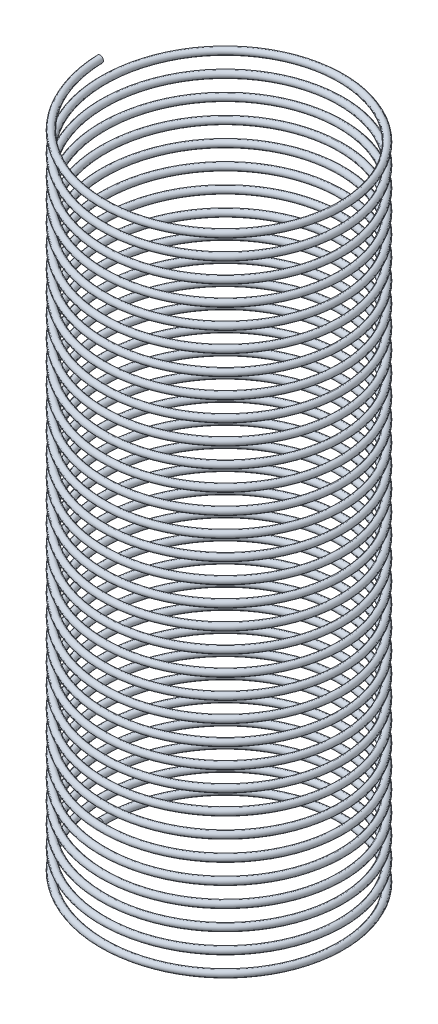
SolidWorks part; units mm, degrees
ref_plane "Front Plane" through (0, 0, 0) normal (0, 0, 1) x (1, 0, 0)
ref_plane "Top Plane" through (0, 0, 0) normal (0, 1, 0) x (1, 0, 0)
ref_plane "Right Plane" through (0, 0, 0) normal (1, 0, 0) x (0, 0, -1)
sketch "Sketch3" plane through (0, 0, 0) normal (0, 1, 0) x (1, 0, 0)
  circle A0 centre (0, 0) radius 17.8101
  dimension "D1" = 35.6203
curve "Helix/Spiral2" pitch 3 height 99 turns 33
sketch "Sketch4" plane through (0, 0, 0) normal (0, 0, 1) x (1, 0, 0)
  circle A0 centre (-17.8101, 0) radius 0.5
  spline S0 degree 3 poles (-17.8101, 0) (-17.8101, 0.0534) (-17.1289, 0.1611) (-14.1784, 0.3219) (-9.6315, 0.4829) (-4.0002, 0.6439) (2.0816, 0.8049) (7.929, 0.9659) (12.8836, 1.1268) (16.3876, 1.2878) (18.0464, 1.4488) (17.6733, 1.6098) (15.3103, 1.7707) (11.2234, 1.9317) (5.8728, 2.0927) (-0.1391, 2.2537) (-6.1353, 2.4146) (-11.4406, 2.5756) (-15.4579, 2.7366) (-17.7346, 2.8976) (-18.0145, 3.0585) (-16.2661, 3.2195) (-12.6862, 3.3805) (-7.6778, 3.5415) (-1.805, 3.7024) (4.271, 3.8634) (9.8662, 4.0244) (14.3504, 4.1854) (17.2189, 4.3463) (18.1486, 4.5073) (17.0349, 4.6683) (14.0031, 4.8293) (9.3946, 4.9902) (3.7284, 5.1512) (-2.3577, 5.3122) (-8.1782, 5.4732) (-13.078, 5.6341) (-16.5052, 5.7951) (-18.0741, 5.9561) (-17.6079, 6.1171) (-15.1591, 6.278) (-11.0034, 6.439) (-5.6089, 6.6) (0.4172, 6.761) (6.3963, 6.922) (11.6552, 7.0829) (15.6018, 7.2439) (17.7917, 7.4049) (17.9784, 7.5659) (16.1407, 7.7268) (12.4857, 7.8878) (7.4249, 8.0488) (1.5281, 8.2098) (-4.5408, 8.3707) (-10.0985, 8.5317) (-14.5191, 8.6927) (-17.3049, 8.8537) (-18.1422, 9.0146) (-16.9369, 9.1756) (-13.8245, 9.3366) (-9.1556, 9.4976) (-3.4557, 9.6585) (2.6332, 9.8195) (8.4256, 9.9805) (13.2693, 10.1415) (16.619, 10.3024) (18.0975, 10.4634) (17.5383, 10.6244) (15.0043, 10.7854) (10.7809, 10.9463) (5.3437, 11.1073) (-0.6952, 11.2683) (-6.6559, 11.4293) (-11.8671, 11.5902) (-15.7421, 11.7512) (-17.8447, 11.9122) (-17.938, 12.0732) (-16.0116, 12.2341) (-12.2824, 12.3951) (-7.1702, 12.5561) (-1.2507, 12.7171) (4.8096, 12.878) (10.3284, 13.039) (14.6843, 13.2) (17.3868, 13.361) (18.1316, 13.522) (16.8349, 13.6829) (13.6426, 13.8439) (8.9143, 14.0049) (3.1823, 14.1659) (-2.9081, 14.3268) (-8.671, 14.4878) (-13.4576, 14.6488) (-16.7289, 14.8098) (-18.1167, 14.9707) (-17.4646, 15.1317) (-14.846, 15.2927) (-10.5559, 15.4537) (-5.0773, 15.6146) (0.9731, 15.7756) (6.9139, 15.9366) (12.0762, 16.0976) (15.8787, 16.2585) (17.8935, 16.4195) (17.8935, 16.5805) (15.8787, 16.7415) (12.0762, 16.9024) (6.9139, 17.0634) (0.9731, 17.2244) (-5.0773, 17.3854) (-10.5559, 17.5463) (-14.846, 17.7073) (-17.4646, 17.8683) (-18.1167, 18.0293) (-16.7289, 18.1902) (-13.4576, 18.3512) (-8.671, 18.5122) (-2.9081, 18.6732) (3.1823, 18.8341) (8.9143, 18.9951) (13.6426, 19.1561) (16.8349, 19.3171) (18.1316, 19.478) (17.3868, 19.639) (14.6843, 19.8) (10.3284, 19.961) (4.8096, 20.122) (-1.2507, 20.2829) (-7.1702, 20.4439) (-12.2824, 20.6049) (-16.0116, 20.7659) (-17.938, 20.9268) (-17.8447, 21.0878) (-15.7421, 21.2488) (-11.8671, 21.4098) (-6.6559, 21.5707) (-0.6952, 21.7317) (5.3437, 21.8927) (10.7809, 22.0537) (15.0043, 22.2146) (17.5383, 22.3756) (18.0975, 22.5366) (16.619, 22.6976) (13.2693, 22.8585) (8.4256, 23.0195) (2.6332, 23.1805) (-3.4557, 23.3415) (-9.1556, 23.5024) (-13.8245, 23.6634) (-16.9369, 23.8244) (-18.1422, 23.9854) (-17.3049, 24.1463) (-14.5191, 24.3073) (-10.0985, 24.4683) (-4.5408, 24.6293) (1.5281, 24.7902) (7.4249, 24.9512) (12.4857, 25.1122) (16.1407, 25.2732) (17.9784, 25.4341) (17.7917, 25.5951) (15.6018, 25.7561) (11.6552, 25.9171) (6.3963, 26.078) (0.4172, 26.239) (-5.6089, 26.4) (-11.0034, 26.561) (-15.1591, 26.722) (-17.6079, 26.8829) (-18.0741, 27.0439) (-16.5052, 27.2049) (-13.078, 27.3659) (-8.1782, 27.5268) (-2.3577, 27.6878) (3.7284, 27.8488) (9.3946, 28.0098) (14.0031, 28.1707) (17.0349, 28.3317) (18.1486, 28.4927) (17.2189, 28.6537) (14.3504, 28.8146) (9.8662, 28.9756) (4.271, 29.1366) (-1.805, 29.2976) (-7.6778, 29.4585) (-12.6862, 29.6195) (-16.2661, 29.7805) (-18.0145, 29.9415) (-17.7346, 30.1024) (-15.4579, 30.2634) (-11.4406, 30.4244) (-6.1353, 30.5854) (-0.1391, 30.7463) (5.8728, 30.9073) (11.2234, 31.0683) (15.3103, 31.2293) (17.6733, 31.3902) (18.0464, 31.5512) (16.3876, 31.7122) (12.8836, 31.8732) (7.929, 32.0341) (2.0816, 32.1951) (-4.0002, 32.3561) (-9.6315, 32.5171) (-14.1784, 32.678) (-17.1289, 32.839) (-18.1507, 33) (-17.1289, 33.161) (-14.1784, 33.322) (-9.6315, 33.4829) (-4.0002, 33.6439) (2.0816, 33.8049) (7.929, 33.9659) (12.8836, 34.1268) (16.3876, 34.2878) (18.0464, 34.4488) (17.6733, 34.6098) (15.3103, 34.7707) (11.2234, 34.9317) (5.8728, 35.0927) (-0.1391, 35.2537) (-6.1353, 35.4146) (-11.4406, 35.5756) (-15.4579, 35.7366) (-17.7346, 35.8976) (-18.0145, 36.0585) (-16.2661, 36.2195) (-12.6862, 36.3805) (-7.6778, 36.5415) (-1.805, 36.7024) (4.271, 36.8634) (9.8662, 37.0244) (14.3504, 37.1854) (17.2189, 37.3463) (18.1486, 37.5073) (17.0349, 37.6683) (14.0031, 37.8293) (9.3946, 37.9902) (3.7284, 38.1512) (-2.3577, 38.3122) (-8.1782, 38.4732) (-13.078, 38.6341) (-16.5052, 38.7951) (-18.0741, 38.9561) (-17.6079, 39.1171) (-15.1591, 39.278) (-11.0034, 39.439) (-5.6089, 39.6) (0.4172, 39.761) (6.3963, 39.922) (11.6552, 40.0829) (15.6018, 40.2439) (17.7917, 40.4049) (17.9784, 40.5659) (16.1407, 40.7268) (12.4857, 40.8878) (7.4249, 41.0488) (1.5281, 41.2098) (-4.5408, 41.3707) (-10.0985, 41.5317) (-14.5191, 41.6927) (-17.3049, 41.8537) (-18.1422, 42.0146) (-16.9369, 42.1756) (-13.8245, 42.3366) (-9.1556, 42.4976) (-3.4557, 42.6585) (2.6332, 42.8195) (8.4256, 42.9805) (13.2693, 43.1415) (16.619, 43.3024) (18.0975, 43.4634) (17.5383, 43.6244) (15.0043, 43.7854) (10.7809, 43.9463) (5.3437, 44.1073) (-0.6952, 44.2683) (-6.6559, 44.4293) (-11.8671, 44.5902) (-15.7421, 44.7512) (-17.8447, 44.9122) (-17.938, 45.0732) (-16.0116, 45.2341) (-12.2824, 45.3951) (-7.1702, 45.5561) (-1.2507, 45.7171) (4.8096, 45.878) (10.3284, 46.039) (14.6843, 46.2) (17.3868, 46.361) (18.1316, 46.522) (16.8349, 46.6829) (13.6426, 46.8439) (8.9143, 47.0049) (3.1823, 47.1659) (-2.9081, 47.3268) (-8.671, 47.4878) (-13.4576, 47.6488) (-16.7289, 47.8098) (-18.1167, 47.9707) (-17.4646, 48.1317) (-14.846, 48.2927) (-10.5559, 48.4537) (-5.0773, 48.6146) (0.9731, 48.7756) (6.9139, 48.9366) (12.0762, 49.0976) (15.8787, 49.2585) (17.8935, 49.4195) (17.8935, 49.5805) (15.8787, 49.7415) (12.0762, 49.9024) (6.9139, 50.0634) (0.9731, 50.2244) (-5.0773, 50.3854) (-10.5559, 50.5463) (-14.846, 50.7073) (-17.4646, 50.8683) (-18.1167, 51.0293) (-16.7289, 51.1902) (-13.4576, 51.3512) (-8.671, 51.5122) (-2.9081, 51.6732) (3.1823, 51.8341) (8.9143, 51.9951) (13.6426, 52.1561) (16.8349, 52.3171) (18.1316, 52.478) (17.3868, 52.639) (14.6843, 52.8) (10.3284, 52.961) (4.8096, 53.122) (-1.2507, 53.2829) (-7.1702, 53.4439) (-12.2824, 53.6049) (-16.0116, 53.7659) (-17.938, 53.9268) (-17.8447, 54.0878) (-15.7421, 54.2488) (-11.8671, 54.4098) (-6.6559, 54.5707) (-0.6952, 54.7317) (5.3437, 54.8927) (10.7809, 55.0537) (15.0043, 55.2146) (17.5383, 55.3756) (18.0975, 55.5366) (16.619, 55.6976) (13.2693, 55.8585) (8.4256, 56.0195) (2.6332, 56.1805) (-3.4557, 56.3415) (-9.1556, 56.5024) (-13.8245, 56.6634) (-16.9369, 56.8244) (-18.1422, 56.9854) (-17.3049, 57.1463) (-14.5191, 57.3073) (-10.0985, 57.4683) (-4.5408, 57.6293) (1.5281, 57.7902) (7.4249, 57.9512) (12.4857, 58.1122) (16.1407, 58.2732) (17.9784, 58.4341) (17.7917, 58.5951) (15.6018, 58.7561) (11.6552, 58.9171) (6.3963, 59.078) (0.4172, 59.239) (-5.6089, 59.4) (-11.0034, 59.561) (-15.1591, 59.722) (-17.6079, 59.8829) (-18.0741, 60.0439) (-16.5052, 60.2049) (-13.078, 60.3659) (-8.1782, 60.5268) (-2.3577, 60.6878) (3.7284, 60.8488) (9.3946, 61.0098) (14.0031, 61.1707) (17.0349, 61.3317) (18.1486, 61.4927) (17.2189, 61.6537) (14.3504, 61.8146) (9.8662, 61.9756) (4.271, 62.1366) (-1.805, 62.2976) (-7.6778, 62.4585) (-12.6862, 62.6195) (-16.2661, 62.7805) (-18.0145, 62.9415) (-17.7346, 63.1024) (-15.4579, 63.2634) (-11.4406, 63.4244) (-6.1353, 63.5854) (-0.1391, 63.7463) (5.8728, 63.9073) (11.2234, 64.0683) (15.3103, 64.2293) (17.6733, 64.3902) (18.0464, 64.5512) (16.3876, 64.7122) (12.8836, 64.8732) (7.929, 65.0341) (2.0816, 65.1951) (-4.0002, 65.3561) (-9.6315, 65.5171) (-14.1784, 65.678) (-17.1289, 65.839) (-18.1507, 66) (-17.1289, 66.161) (-14.1784, 66.322) (-9.6315, 66.4829) (-4.0002, 66.6439) (2.0816, 66.8049) (7.929, 66.9659) (12.8836, 67.1268) (16.3876, 67.2878) (18.0464, 67.4488) (17.6733, 67.6098) (15.3103, 67.7707) (11.2234, 67.9317) (5.8728, 68.0927) (-0.1391, 68.2537) (-6.1353, 68.4146) (-11.4406, 68.5756) (-15.4579, 68.7366) (-17.7346, 68.8976) (-18.0145, 69.0585) (-16.2661, 69.2195) (-12.6862, 69.3805) (-7.6778, 69.5415) (-1.805, 69.7024) (4.271, 69.8634) (9.8662, 70.0244) (14.3504, 70.1854) (17.2189, 70.3463) (18.1486, 70.5073) (17.0349, 70.6683) (14.0031, 70.8293) (9.3946, 70.9902) (3.7284, 71.1512) (-2.3577, 71.3122) (-8.1782, 71.4732) (-13.078, 71.6341) (-16.5052, 71.7951) (-18.0741, 71.9561) (-17.6079, 72.1171) (-15.1591, 72.278) (-11.0034, 72.439) (-5.6089, 72.6) (0.4172, 72.761) (6.3963, 72.922) (11.6552, 73.0829) (15.6018, 73.2439) (17.7917, 73.4049) (17.9784, 73.5659) (16.1407, 73.7268) (12.4857, 73.8878) (7.4249, 74.0488) (1.5281, 74.2098) (-4.5408, 74.3707) (-10.0985, 74.5317) (-14.5191, 74.6927) (-17.3049, 74.8537) (-18.1422, 75.0146) (-16.9369, 75.1756) (-13.8245, 75.3366) (-9.1556, 75.4976) (-3.4557, 75.6585) (2.6332, 75.8195) (8.4256, 75.9805) (13.2693, 76.1415) (16.619, 76.3024) (18.0975, 76.4634) (17.5383, 76.6244) (15.0043, 76.7854) (10.7809, 76.9463) (5.3437, 77.1073) (-0.6952, 77.2683) (-6.6559, 77.4293) (-11.8671, 77.5902) (-15.7421, 77.7512) (-17.8447, 77.9122) (-17.938, 78.0732) (-16.0116, 78.2341) (-12.2824, 78.3951) (-7.1702, 78.5561) (-1.2507, 78.7171) (4.8096, 78.878) (10.3284, 79.039) (14.6843, 79.2) (17.3868, 79.361) (18.1316, 79.522) (16.8349, 79.6829) (13.6426, 79.8439) (8.9143, 80.0049) (3.1823, 80.1659) (-2.9081, 80.3268) (-8.671, 80.4878) (-13.4576, 80.6488) (-16.7289, 80.8098) (-18.1167, 80.9707) (-17.4646, 81.1317) (-14.846, 81.2927) (-10.5559, 81.4537) (-5.0773, 81.6146) (0.9731, 81.7756) (6.9139, 81.9366) (12.0762, 82.0976) (15.8787, 82.2585) (17.8935, 82.4195) (17.8935, 82.5805) (15.8787, 82.7415) (12.0762, 82.9024) (6.9139, 83.0634) (0.9731, 83.2244) (-5.0773, 83.3854) (-10.5559, 83.5463) (-14.846, 83.7073) (-17.4646, 83.8683) (-18.1167, 84.0293) (-16.7289, 84.1902) (-13.4576, 84.3512) (-8.671, 84.5122) (-2.9081, 84.6732) (3.1823, 84.8341) (8.9143, 84.9951) (13.6426, 85.1561) (16.8349, 85.3171) (18.1316, 85.478) (17.3868, 85.639) (14.6843, 85.8) (10.3284, 85.961) (4.8096, 86.122) (-1.2507, 86.2829) (-7.1702, 86.4439) (-12.2824, 86.6049) (-16.0116, 86.7659) (-17.938, 86.9268) (-17.8447, 87.0878) (-15.7421, 87.2488) (-11.8671, 87.4098) (-6.6559, 87.5707) (-0.6952, 87.7317) (5.3437, 87.8927) (10.7809, 88.0537) (15.0043, 88.2146) (17.5383, 88.3756) (18.0975, 88.5366) (16.619, 88.6976) (13.2693, 88.8585) (8.4256, 89.0195) (2.6332, 89.1805) (-3.4557, 89.3415) (-9.1556, 89.5024) (-13.8245, 89.6634) (-16.9369, 89.8244) (-18.1422, 89.9854) (-17.3049, 90.1463) (-14.5191, 90.3073) (-10.0985, 90.4683) (-4.5408, 90.6293) (1.5281, 90.7902) (7.4249, 90.9512) (12.4857, 91.1122) (16.1407, 91.2732) (17.9784, 91.4341) (17.7917, 91.5951) (15.6018, 91.7561) (11.6552, 91.9171) (6.3963, 92.078) (0.4172, 92.239) (-5.6089, 92.4) (-11.0034, 92.561) (-15.1591, 92.722) (-17.6079, 92.8829) (-18.0741, 93.0439) (-16.5052, 93.2049) (-13.078, 93.3659) (-8.1782, 93.5268) (-2.3577, 93.6878) (3.7284, 93.8488) (9.3946, 94.0098) (14.0031, 94.1707) (17.0349, 94.3317) (18.1486, 94.4927) (17.2189, 94.6537) (14.3504, 94.8146) (9.8662, 94.9756) (4.271, 95.1366) (-1.805, 95.2976) (-7.6778, 95.4585) (-12.6862, 95.6195) (-16.2661, 95.7805) (-18.0145, 95.9415) (-17.7346, 96.1024) (-15.4579, 96.2634) (-11.4406, 96.4244) (-6.1353, 96.5854) (-0.1391, 96.7463) (5.8728, 96.9073) (11.2234, 97.0683) (15.3103, 97.2293) (17.6733, 97.3902) (18.0464, 97.5512) (16.3876, 97.7122) (12.8836, 97.8732) (7.929, 98.0341) (2.0816, 98.1951) (-4.0002, 98.3561) (-9.6315, 98.5171) (-14.1784, 98.6781) (-17.1289, 98.8389) (-17.8101, 98.9466) (-17.8101, 99) knots 0 0 0 0 0.001626 0.003252 0.004878 0.006504 0.00813 0.009756 0.011382 0.013008 0.014634 0.01626 0.017886 0.019512 0.021138 0.022764 0.02439 0.026016 0.027642 0.029268 0.030894 0.03252 0.034146 0.035772 0.037398 0.039024 0.04065 0.042276 0.043902 0.045528 0.047154 0.04878 0.050407 0.052033 0.053659 0.055285 0.056911 0.058537 0.060163 0.061789 0.063415 0.065041 0.066667 0.068293 0.069919 0.071545 0.073171 0.074797 0.076423 0.078049 0.079675 0.081301 0.082927 0.084553 0.086179 0.087805 0.089431 0.091057 0.092683 0.094309 0.095935 0.097561 0.099187 0.100813 0.102439 0.104065 0.105691 0.107317 0.108943 0.110569 0.112195 0.113821 0.115447 0.117073 0.118699 0.120325 0.121951 0.123577 0.125203 0.126829 0.128455 0.130081 0.131707 0.133333 0.134959 0.136585 0.138211 0.139837 0.141463 0.143089 0.144715 0.146341 0.147967 0.149593 0.15122 0.152846 0.154472 0.156098 0.157724 0.15935 0.160976 0.162602 0.164228 0.165854 0.16748 0.169106 0.170732 0.172358 0.173984 0.17561 0.177236 0.178862 0.180488 0.182114 0.18374 0.185366 0.186992 0.188618 0.190244 0.19187 0.193496 0.195122 0.196748 0.198374 0.2 0.201626 0.203252 0.204878 0.206504 0.20813 0.209756 0.211382 0.213008 0.214634 0.21626 0.217886 0.219512 0.221138 0.222764 0.22439 0.226016 0.227642 0.229268 0.230894 0.23252 0.234146 0.235772 0.237398 0.239024 0.24065 0.242276 0.243902 0.245528 0.247154 0.24878 0.250407 0.252033 0.253659 0.255285 0.256911 0.258537 0.260163 0.261789 0.263415 0.265041 0.266667 0.268293 0.269919 0.271545 0.273171 0.274797 0.276423 0.278049 0.279675 0.281301 0.282927 0.284553 0.286179 0.287805 0.289431 0.291057 0.292683 0.294309 0.295935 0.297561 0.299187 0.300813 0.302439 0.304065 0.305691 0.307317 0.308943 0.310569 0.312195 0.313821 0.315447 0.317073 0.318699 0.320325 0.321951 0.323577 0.325203 0.326829 0.328455 0.330081 0.331707 0.333333 0.334959 0.336585 0.338211 0.339837 0.341463 0.343089 0.344715 0.346341 0.347967 0.349593 0.35122 0.352846 0.354472 0.356098 0.357724 0.35935 0.360976 0.362602 0.364228 0.365854 0.36748 0.369106 0.370732 0.372358 0.373984 0.37561 0.377236 0.378862 0.380488 0.382114 0.38374 0.385366 0.386992 0.388618 0.390244 0.39187 0.393496 0.395122 0.396748 0.398374 0.4 0.401626 0.403252 0.404878 0.406504 0.40813 0.409756 0.411382 0.413008 0.414634 0.41626 0.417886 0.419512 0.421138 0.422764 0.42439 0.426016 0.427642 0.429268 0.430894 0.43252 0.434146 0.435772 0.437398 0.439024 0.44065 0.442276 0.443902 0.445528 0.447154 0.44878 0.450407 0.452033 0.453659 0.455285 0.456911 0.458537 0.460163 0.461789 0.463415 0.465041 0.466667 0.468293 0.469919 0.471545 0.473171 0.474797 0.476423 0.478049 0.479675 0.481301 0.482927 0.484553 0.486179 0.487805 0.489431 0.491057 0.492683 0.494309 0.495935 0.497561 0.499187 0.500813 0.502439 0.504065 0.505691 0.507317 0.508943 0.510569 0.512195 0.513821 0.515447 0.517073 0.518699 0.520325 0.521951 0.523577 0.525203 0.526829 0.528455 0.530081 0.531707 0.533333 0.534959 0.536585 0.538211 0.539837 0.541463 0.543089 0.544715 0.546341 0.547967 0.549593 0.55122 0.552846 0.554472 0.556098 0.557724 0.55935 0.560976 0.562602 0.564228 0.565854 0.56748 0.569106 0.570732 0.572358 0.573984 0.57561 0.577236 0.578862 0.580488 0.582114 0.58374 0.585366 0.586992 0.588618 0.590244 0.59187 0.593496 0.595122 0.596748 0.598374 0.6 0.601626 0.603252 0.604878 0.606504 0.60813 0.609756 0.611382 0.613008 0.614634 0.61626 0.617886 0.619512 0.621138 0.622764 0.62439 0.626016 0.627642 0.629268 0.630894 0.63252 0.634146 0.635772 0.637398 0.639024 0.64065 0.642276 0.643902 0.645528 0.647154 0.64878 0.650407 0.652033 0.653659 0.655285 0.656911 0.658537 0.660163 0.661789 0.663415 0.665041 0.666667 0.668293 0.669919 0.671545 0.673171 0.674797 0.676423 0.678049 0.679675 0.681301 0.682927 0.684553 0.686179 0.687805 0.689431 0.691057 0.692683 0.694309 0.695935 0.697561 0.699187 0.700813 0.702439 0.704065 0.705691 0.707317 0.708943 0.710569 0.712195 0.713821 0.715447 0.717073 0.718699 0.720325 0.721951 0.723577 0.725203 0.726829 0.728455 0.730081 0.731707 0.733333 0.734959 0.736585 0.738211 0.739837 0.741463 0.743089 0.744715 0.746341 0.747967 0.749593 0.75122 0.752846 0.754472 0.756098 0.757724 0.75935 0.760976 0.762602 0.764228 0.765854 0.76748 0.769106 0.770732 0.772358 0.773984 0.77561 0.777236 0.778862 0.780488 0.782114 0.78374 0.785366 0.786992 0.788618 0.790244 0.79187 0.793496 0.795122 0.796748 0.798374 0.8 0.801626 0.803252 0.804878 0.806504 0.80813 0.809756 0.811382 0.813008 0.814634 0.81626 0.817886 0.819512 0.821138 0.822764 0.82439 0.826016 0.827642 0.829268 0.830894 0.83252 0.834146 0.835772 0.837398 0.839024 0.84065 0.842276 0.843902 0.845528 0.847154 0.84878 0.850407 0.852033 0.853659 0.855285 0.856911 0.858537 0.860163 0.861789 0.863415 0.865041 0.866667 0.868293 0.869919 0.871545 0.873171 0.874797 0.876423 0.878049 0.879675 0.881301 0.882927 0.884553 0.886179 0.887805 0.889431 0.891057 0.892683 0.894309 0.895935 0.897561 0.899187 0.900813 0.902439 0.904065 0.905691 0.907317 0.908943 0.910569 0.912195 0.913821 0.915447 0.917073 0.918699 0.920325 0.921951 0.923577 0.925203 0.926829 0.928455 0.930081 0.931707 0.933333 0.934959 0.936585 0.938211 0.939837 0.941463 0.943089 0.944715 0.946341 0.947967 0.949593 0.95122 0.952846 0.954472 0.956098 0.957724 0.95935 0.960976 0.962602 0.964228 0.965854 0.96748 0.969106 0.970732 0.972358 0.973984 0.97561 0.977236 0.978862 0.980488 0.982114 0.98374 0.985366 0.986992 0.988618 0.990244 0.99187 0.993496 0.995122 0.996748 0.998374 1 1 1 1 construction
  point P2 (0, 0)
  point P3 (0, 0)
  point P6 (0, 0)
  dimension "D1" = 1
sweep "Sweep1" add profiles "Sketch4" path "Helix/Spiral2"
